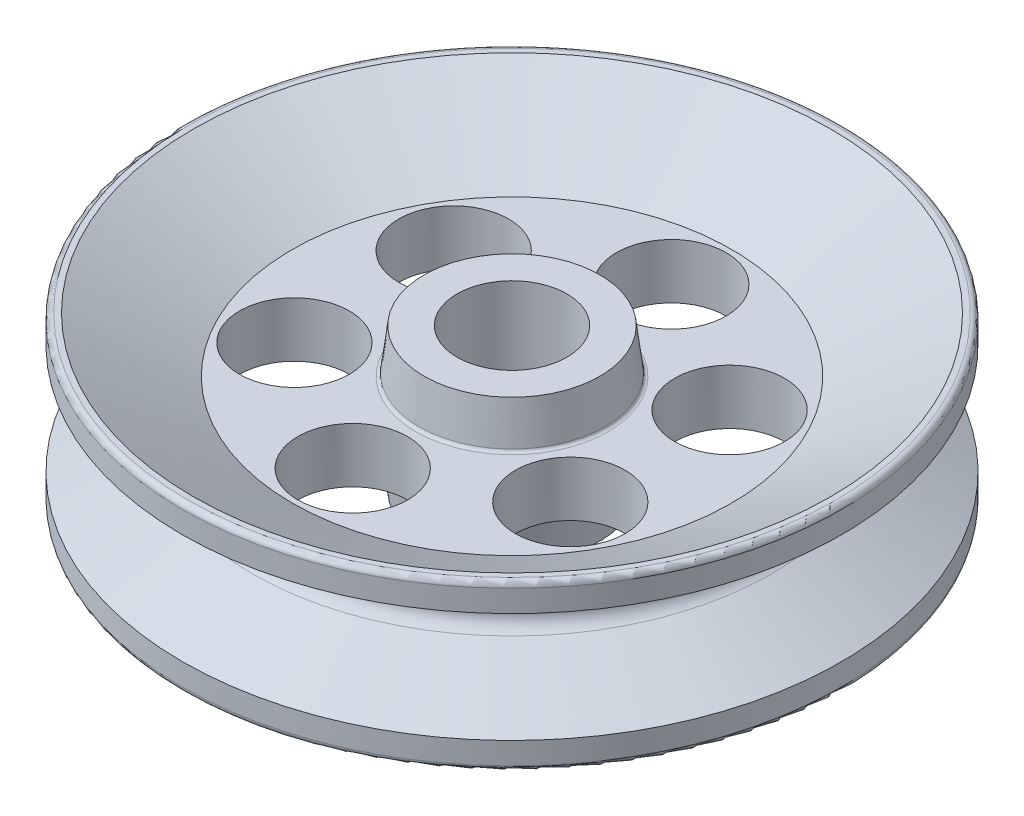
SolidWorks part; units mm, degrees
ref_plane "Front Plane" through (0, 0, 0) normal (0, 0, 1) x (1, 0, 0)
ref_plane "Top Plane" through (0, 0, 0) normal (0, 1, 0) x (1, 0, 0)
ref_plane "Right Plane" through (0, 0, 0) normal (1, 0, 0) x (0, 0, -1)
sketch "Sketch1" plane through (0, 0, 0) normal (0, 1, 0) x (1, 0, 0)
  circle A0 centre (0, 0) radius 1524
extrude "Boss-Extrude1" add sketch "Sketch1" along normal mid plane 762
sketch "Sketch2" plane through (0, 0, 0) normal (1, 0, 0) x (0, 0, -1)
  line L0 (1524, -254) -> (1524, 254)
  line L2 (1524, -381) -> (1524, 381) construction
  line L3 (1524, 254) -> (1198.3591, 65.9911)
  line L5 (1676.4, 0) -> (-1676.4, 0) construction
  line L7 (1524, -254) -> (1198.3591, -65.9911)
  arc A0 (1198.3591, 65.9911) -> (1198.3591, -65.9911) centre (1236.4591, 0) ccw
  dimension "D1" = 254
revolve "Cut-Revolve1" cut sketch "Sketch2" angle 360 about axis through (0, 381, 0) along (0, -1, 0)
sketch "Sketch3" plane through (0, 381, 0) normal (0, 1, 0) x (1, 0, 0)
  circle A0 centre (0, 0) radius 254
  dimension "D1" = 508
extrude "Cut-Extrude1" cut sketch "Sketch3" against normal through all
sketch "Sketch4" plane through (0, 381, 0) normal (0, 1, 0) x (1, 0, 0)
  circle A0 centre (0, 0) radius 736.6 construction
  circle A1 centre (0, 736.6) radius 254
  dimension "D1" = 736.6
  dimension "D2" = 508
extrude "Cut-Extrude2" cut sketch "Sketch4" against normal through all
pattern_circular "CirPattern1" count 6 every 60 about axis through (0, 0, 0) along (0, 1, 0) of "Cut-Extrude2"
sketch "Sketch7" plane through (0, 0, 0) normal (1, 0, 0) x (0, 0, -1)
  line L1 (406.4, 330.2) -> (430.1375, 139.684)
  line L2 (-1524, -381) -> (1524, -381) construction
  line L3 (0, -330.2) -> (0, -381)
  line L4 (1473.2, -381) -> (0, -381)
  line L5 (406.4, -330.2) -> (430.1375, -139.684)
  line L6 (1524, -381) -> (1524, -254) construction
  line L7 (0, -330.2) -> (406.4, -330.2)
  line L8 (1473.2, -381) -> (1016, -127)
  line L9 (1016, 127) -> (444.5, 127)
  line L10 (1473.2, 381) -> (1016, 127)
  line L11 (1016, -127) -> (444.5, -127)
  line L12 (1473.2, 381) -> (0, 381)
  line L13 (0, 330.2) -> (0, 381)
  line L14 (0, 330.2) -> (406.4, 330.2)
  arc A1 (444.5, -127) -> (430.1375, -139.684) centre (444.5, -141.4735) ccw
  arc A2 (444.5, 127) -> (430.1375, 139.684) centre (444.5, 141.4735) cw
  point P7 (1473.2, -381)
  dimension "D1" = 50.8
  dimension "D2" = 50.8
revolve "Cut-Revolve3" cut sketch "Sketch7" angle 360 about axis through (0, 254, 0) along (0, 1, 0)
fillet "Fillet3" radius 25.4 2 edges at (0, 381, 1524) (0, -381, 1524)
